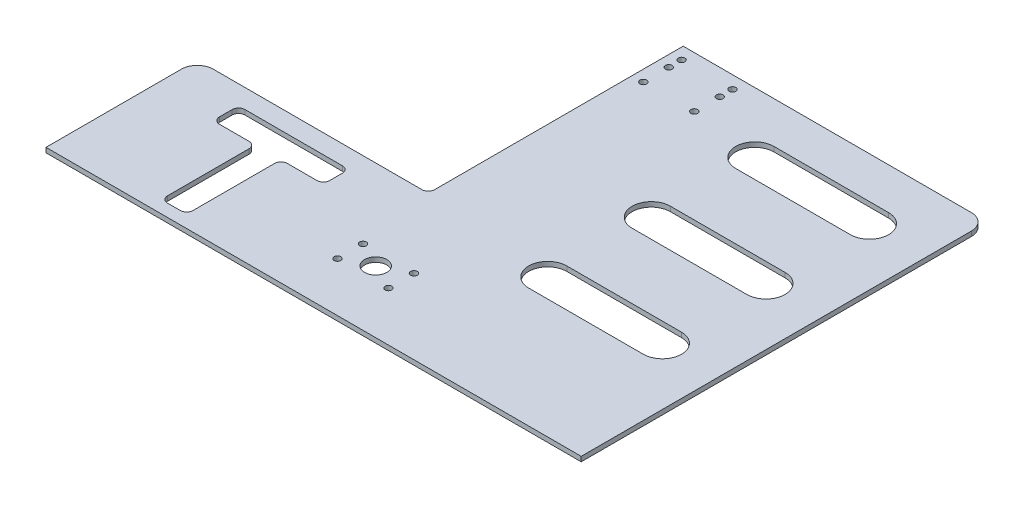
SolidWorks part; units mm, degrees
ref_plane "Front Plane" through (0, 0, 0) normal (0, 0, 1) x (1, 0, 0)
ref_plane "Top Plane" through (0, 0, 0) normal (0, 1, 0) x (1, 0, 0)
ref_plane "Right Plane" through (0, 0, 0) normal (1, 0, 0) x (0, 0, -1)
sketch "Sketch1" plane through (0, 0, 0) normal (0, 1, 0) x (1, 0, 0)
  line L0 (0, 0) -> (0, -43) construction
  line L1 (-23, 216) -> (158, 216)
  line L2 (-168, 46) -> (-168, -43)
  line L3 (-168, -43) -> (168, -43)
  line L4 (168, 206) -> (168, -43)
  line L5 (16, -8) -> (16, 8) construction
  line L6 (-27, 56) -> (-158, 56)
  line L7 (-103.5, -27.19) -> (-103.5, 24)
  line L8 (-126.1097, 44) -> (-64.8903, 44)
  line L9 (-130.1097, 40) -> (-130.1097, 32)
  line L10 (-126.1097, 28) -> (-107.5, 28)
  line L11 (-60.8903, 40) -> (-60.8903, 32)
  line L12 (-130.1097, 44) -> (-60.8903, 28) construction
  line L13 (-130.1097, 28) -> (-60.8903, 44) construction
  line L14 (-99.5, -31.19) -> (-91.5, -31.19)
  line L16 (-87.5, -27.19) -> (-87.5, 24)
  line L17 (-83.5, 28) -> (-64.8903, 28)
  line L18 (-16, -8) -> (-16, 8) construction
  line L19 (-23, 216) -> (-23, 60)
  line L20 (60, 48) -> (132, 48) construction
  line L21 (60, 60) -> (132, 60)
  line L22 (60, 36) -> (132, 36)
  line L23 (60, 113) -> (132, 113) construction
  line L24 (60, 125) -> (132, 125)
  line L25 (60, 101) -> (132, 101)
  line L26 (60, 178) -> (132, 178) construction
  line L27 (60, 190) -> (132, 190)
  line L28 (60, 166) -> (132, 166)
  circle A0 centre (0, 0) radius 7
  circle A1 centre (16, 8) radius 2.1
  circle A2 centre (16, -8) radius 2.1
  circle A3 centre (16, 208) radius 2.1
  circle A4 centre (16, 184) radius 2.1
  circle A5 centre (16, 200) radius 2.1
  arc A6 (-87.5, -27.19) -> (-91.5, -31.19) centre (-91.5, -27.19) cw
  arc A7 (-99.5, -31.19) -> (-103.5, -27.19) centre (-99.5, -27.19) cw
  arc A8 (-87.5, 24) -> (-83.5, 28) centre (-83.5, 24) cw
  arc A9 (-103.5, 24) -> (-107.5, 28) centre (-107.5, 24) ccw
  arc A10 (-60.8903, 32) -> (-64.8903, 28) centre (-64.8903, 32) cw
  arc A11 (-60.8903, 40) -> (-64.8903, 44) centre (-64.8903, 40) ccw
  arc A12 (-126.1097, 28) -> (-130.1097, 32) centre (-126.1097, 32) cw
  arc A13 (-130.1097, 40) -> (-126.1097, 44) centre (-126.1097, 40) cw
  arc A14 (-27, 56) -> (-23, 60) centre (-27, 60) ccw
  arc A15 (-158, 56) -> (-168, 46) centre (-158, 46) ccw
  arc A16 (158, 216) -> (168, 206) centre (158, 206) cw
  circle A17 centre (-16, 184) radius 2.1
  circle A18 centre (-16, 200) radius 2.1
  circle A19 centre (-16, 208) radius 2.1
  circle A20 centre (-16, -8) radius 2.1
  circle A21 centre (-16, 8) radius 2.1
  arc A24 (60, 60) -> (60, 36) centre (60, 48) ccw
  arc A25 (132, 36) -> (132, 60) centre (132, 48) ccw
  arc A26 (60, 125) -> (60, 101) centre (60, 113) ccw
  arc A27 (132, 101) -> (132, 125) centre (132, 113) ccw
  arc A28 (60, 190) -> (60, 166) centre (60, 178) ccw
  arc A29 (132, 166) -> (132, 190) centre (132, 178) ccw
  point P0 (0, 0)
  point P8 (0, 8)
  point P9 (16, 8)
  point P16 (0, 216)
  point P17 (0, 192)
  point P26 (0, 56)
  point P29 (-95.5, 36)
  point P76 (96, 48)
  point P79 (96, 48)
  point P88 (96, 113)
  point P95 (96, 178)
  dimension "D3" = 56
  dimension "D7" = 4.2
  dimension "D12" = 4.2
  dimension "D22" = 4
  dimension "D23" = 4
  dimension "D24" = 10
  dimension "D25" = 10
  dimension "D26" = 48
  dimension "D28" = 72
  dimension "D29" = 12
  dimension "D1" = 336
  dimension "D2" = 43
  dimension "D4" = 216
  dimension "D5" = 8
  dimension "D6" = 16
  dimension "D8" = 8
  dimension "D9" = 216
  dimension "D10" = 24
  dimension "D11" = 8
  dimension "D13" = 8
  dimension "D14" = 8
  dimension "D15" = 8
  dimension "D16" = 8
  dimension "D17" = 16
  dimension "D18" = 12
  dimension "D19" = 7
  dimension "D20" = 64.5
  dimension "D21" = 168
  dimension "D27" = 72
  dimension "D30" = 3
extrude "Boss-Extrude1" add sketch "Sketch1" along normal blind 3
sketch "Sketch2" plane through (0, 3, 0) normal (0, 1, 0) x (1, 0, 0)
  line L0 (-168, -43) -> (-168, -39)
  line L1 (-168, 46) -> (-168, -43) construction
  line L2 (-168, -39) -> (168, -39)
  line L3 (168, -43) -> (168, 206) construction
  line L4 (168, -39) -> (168, -43)
  line L5 (-168, -43) -> (168, -43) construction
  line L6 (168, -43) -> (-168, -43)
  dimension "D1" = 4
extrude "Cut-Extrude1" cut sketch "Sketch2" against normal through all both and the other way through all
